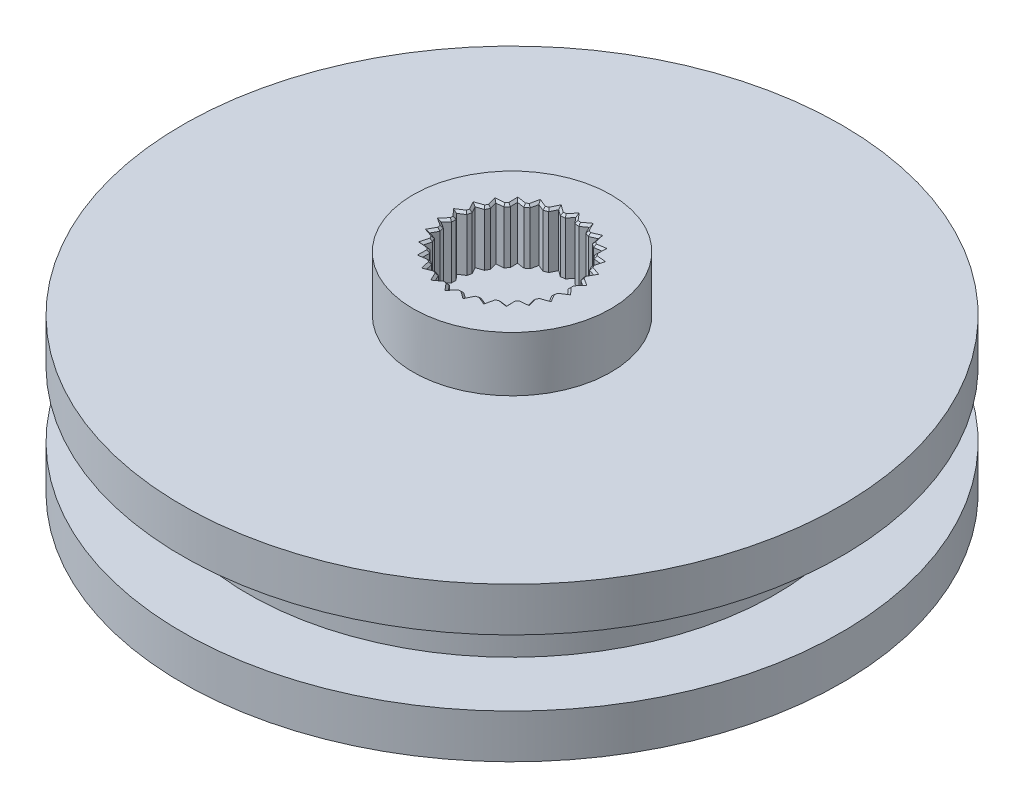
SolidWorks part; units mm, degrees
ref_plane "Front Plane" through (0, 0, 0) normal (0, 0, 1) x (1, 0, 0)
ref_plane "Top Plane" through (0, 0, 0) normal (0, 1, 0) x (1, 0, 0)
ref_plane "Right Plane" through (0, 0, 0) normal (1, 0, 0) x (0, 0, -1)
sketch "Sketch1" plane through (0, 0, 0) normal (0, 1, 0) x (1, 0, 0)
  line L0 (-4.9497, 4.9497) -> (4.9497, 4.9497) construction
  line L1 (4.9497, 4.9497) -> (4.9497, -4.9497) construction
  circle A0 centre (0, 0) radius 10
  circle A1 centre (-4.9497, 4.9497) radius 1.25
  circle A2 centre (4.9497, 4.9497) radius 1.25
  circle A3 centre (4.9497, -4.9497) radius 1.25
  circle A4 centre (-4.9497, -4.9497) radius 1.25
  circle A5 centre (0, 0) radius 7 construction
  circle A6 centre (0, 0) radius 1.5
  dimension "D1" = 20
  dimension "D2" = 2.5
  dimension "D3" = 3
  dimension "D4" = 14
extrude "Boss-Extrude1" add sketch "Sketch1" along normal blind 2
cosmetic thread "Cosmetic Thread1" parameters "D2"=3
cosmetic thread "Cosmetic Thread2" parameters "D2"=3
cosmetic thread "Cosmetic Thread3" parameters "D2"=3
cosmetic thread "Cosmetic Thread4" parameters "D2"=3
sketch "Sketch2" plane through (0, 2, 0) normal (0, 1, 0) x (1, 0, 0)
  circle A0 centre (0, 0) radius 4.5
  circle A1 centre (0, 0) radius 1.5 construction
  circle A2 centre (0, 0) radius 1.5
  dimension "D1" = 9
extrude "Boss-Extrude2" add sketch "Sketch2" along normal blind 2.5
sketch "Sketch3" plane through (0, 4.5, 0) normal (0, 1, 0) x (1, 0, 0)
  circle A0 centre (0, 0) radius 2.25
  dimension "D1" = 4.5
extrude "Cut-Extrude1" cut sketch "Sketch3" against normal blind 3.6
sketch "Sketch7" plane through (0, 4.5, 0) normal (0, 1, 0) x (1, 0, 0)
  line L0 (-1.035, 2.4395) -> (-0.843, 2.5123)
  line L1 (-0.843, 2.5123) -> (-0.7982, 2.6036)
  line L2 (-0.7982, 2.6036) -> (-0.694, 2.8157)
  line L3 (-0.694, 2.8157) -> (-0.5032, 2.6763)
  line L4 (-0.5032, 2.6763) -> (-0.4211, 2.6163)
  line L5 (-0.4211, 2.6163) -> (-0.2173, 2.6411)
  line L6 (-0.2173, 2.6411) -> (-0.1519, 2.719)
  line L7 (-0.1519, 2.719) -> (0, 2.9)
  line L8 (0, 2.9) -> (0.1519, 2.719)
  line L9 (0.1519, 2.719) -> (0.2173, 2.6411)
  line L10 (0.2173, 2.6411) -> (0.4211, 2.6163)
  line L11 (0.4211, 2.6163) -> (0.5032, 2.6763)
  line L12 (0.5032, 2.6763) -> (0.694, 2.8157)
  line L13 (0.694, 2.8157) -> (0.7982, 2.6036)
  line L14 (0.7982, 2.6036) -> (0.843, 2.5123)
  line L15 (0.843, 2.5123) -> (1.035, 2.4395)
  line L16 (1.035, 2.4395) -> (1.1291, 2.4781)
  line L17 (1.1291, 2.4781) -> (1.3477, 2.5678)
  line L18 (1.3477, 2.5678) -> (1.3981, 2.337)
  line L19 (1.3981, 2.337) -> (1.4197, 2.2376)
  line L20 (1.4197, 2.2376) -> (1.5887, 2.1209)
  line L21 (1.5887, 2.1209) -> (1.6893, 2.1359)
  line L22 (1.6893, 2.1359) -> (1.9231, 2.1707)
  line L23 (1.9231, 2.1707) -> (1.9167, 1.9345)
  line L24 (1.9167, 1.9345) -> (1.914, 1.8328)
  line L25 (1.914, 1.8328) -> (2.0501, 1.6791)
  line L26 (2.0501, 1.6791) -> (2.1514, 1.6696)
  line L27 (2.1514, 1.6696) -> (2.3867, 1.6474)
  line L28 (2.3867, 1.6474) -> (2.324, 1.4196)
  line L29 (2.324, 1.4196) -> (2.297, 1.3215)
  line L30 (2.297, 1.3215) -> (2.3924, 1.1397)
  line L31 (2.3924, 1.1397) -> (2.4884, 1.1062)
  line L32 (2.4884, 1.1062) -> (2.7115, 1.0284)
  line L33 (2.7115, 1.0284) -> (2.5962, 0.8221)
  line L34 (2.5962, 0.8221) -> (2.5465, 0.7334)
  line L35 (2.5465, 0.7334) -> (2.5956, 0.534)
  line L36 (2.6809, 0.4785) -> (2.5956, 0.534) construction
  line L37 (2.5956, 0.534) -> (2.6809, 0.4785)
  line L38 (2.6809, 0.4785) -> (2.8789, 0.3496)
  line L39 (2.6809, 0.4785) -> (2.8789, 0.3496)
  line L40 (2.7175, 0.177) -> (2.648, 0.1027)
  line L41 (2.648, 0.1027) -> (2.648, -0.1027)
  line L42 (2.648, -0.1027) -> (2.7175, -0.177)
  line L43 (2.7175, -0.177) -> (2.8789, -0.3496)
  line L44 (2.8789, -0.3496) -> (2.6809, -0.4785)
  line L45 (2.6809, -0.4785) -> (2.5956, -0.534)
  line L46 (2.5956, -0.534) -> (2.5465, -0.7334)
  line L47 (2.5465, -0.7334) -> (2.5962, -0.8221)
  line L48 (2.5962, -0.8221) -> (2.7115, -1.0284)
  line L49 (2.7115, -1.0284) -> (2.4884, -1.1062)
  line L50 (2.4884, -1.1062) -> (2.3924, -1.1397)
  line L51 (2.3924, -1.1397) -> (2.4884, -1.1062) construction
  line L52 (2.3924, -1.1397) -> (2.297, -1.3215)
  line L53 (2.297, -1.3215) -> (2.324, -1.4196)
  line L54 (2.324, -1.4196) -> (2.3867, -1.6474)
  line L55 (2.3867, -1.6474) -> (2.1514, -1.6696)
  line L56 (2.1514, -1.6696) -> (2.0501, -1.6791)
  line L57 (2.0501, -1.6791) -> (1.914, -1.8328)
  line L58 (1.914, -1.8328) -> (1.9167, -1.9345)
  line L59 (1.9167, -1.9345) -> (1.9231, -2.1707)
  line L60 (1.9231, -2.1707) -> (1.6893, -2.1359)
  line L61 (1.6893, -2.1359) -> (1.5887, -2.1209)
  line L62 (1.5887, -2.1209) -> (1.4197, -2.2376)
  line L63 (1.4197, -2.2376) -> (1.3981, -2.337)
  line L64 (1.3981, -2.337) -> (1.3477, -2.5678)
  line L65 (1.3477, -2.5678) -> (1.1291, -2.4781)
  line L66 (1.1291, -2.4781) -> (1.035, -2.4395)
  line L67 (1.035, -2.4395) -> (0.843, -2.5123)
  line L68 (0.843, -2.5123) -> (0.7982, -2.6036)
  line L69 (0.7982, -2.6036) -> (0.694, -2.8157)
  line L70 (0.694, -2.8157) -> (0.5032, -2.6763)
  line L71 (0.5032, -2.6763) -> (0.4211, -2.6163)
  line L72 (0.4211, -2.6163) -> (0.2173, -2.6411)
  line L73 (0.2173, -2.6411) -> (0.1519, -2.719)
  line L74 (0.1519, -2.719) -> (0, -2.9)
  line L75 (0, -2.9) -> (-0.1519, -2.719)
  line L76 (-0.1519, -2.719) -> (-0.2173, -2.6411)
  line L77 (-0.2173, -2.6411) -> (-0.4211, -2.6163)
  line L78 (-0.4211, -2.6163) -> (-0.5032, -2.6763)
  line L79 (-0.5032, -2.6763) -> (-0.694, -2.8157)
  line L80 (-0.694, -2.8157) -> (-0.7982, -2.6036)
  line L81 (-0.7982, -2.6036) -> (-0.843, -2.5123)
  line L82 (-0.843, -2.5123) -> (-1.035, -2.4395)
  line L83 (-1.035, -2.4395) -> (-1.1291, -2.4781)
  line L84 (-1.1291, -2.4781) -> (-1.3477, -2.5678)
  line L85 (-1.3477, -2.5678) -> (-1.3981, -2.337)
  line L86 (-1.3981, -2.337) -> (-1.4197, -2.2376)
  line L87 (-1.4197, -2.2376) -> (-1.5887, -2.1209)
  line L88 (-1.5887, -2.1209) -> (-1.6893, -2.1359)
  line L89 (-1.6893, -2.1359) -> (-1.9231, -2.1707)
  line L90 (-1.9231, -2.1707) -> (-1.9167, -1.9345)
  line L91 (-1.9167, -1.9345) -> (-1.914, -1.8328)
  line L92 (-1.914, -1.8328) -> (-2.0501, -1.6791)
  line L93 (-2.0501, -1.6791) -> (-2.1514, -1.6696)
  line L94 (-2.1514, -1.6696) -> (-2.3867, -1.6474)
  line L95 (-2.3867, -1.6474) -> (-2.324, -1.4196)
  line L96 (-2.324, -1.4196) -> (-2.297, -1.3215)
  line L97 (-2.297, -1.3215) -> (-2.3924, -1.1397)
  line L98 (-2.3924, -1.1397) -> (-2.4884, -1.1062)
  line L99 (-2.4884, -1.1062) -> (-2.7115, -1.0284)
  line L100 (-2.7115, -1.0284) -> (-2.5962, -0.8221)
  line L101 (-2.5962, -0.8221) -> (-2.5465, -0.7334)
  line L102 (-2.5465, -0.7334) -> (-2.5956, -0.534)
  line L103 (-2.5956, -0.534) -> (-2.6809, -0.4785)
  line L104 (-2.6809, -0.4785) -> (-2.8789, -0.3496)
  line L105 (-2.8789, -0.3496) -> (-2.7175, -0.177)
  line L106 (-2.7175, -0.177) -> (-2.648, -0.1027)
  line L107 (-2.648, -0.1027) -> (-2.648, 0.1027)
  line L108 (-2.648, 0.1027) -> (-2.7175, 0.177)
  line L109 (-2.7175, 0.177) -> (-2.8789, 0.3496)
  line L110 (-2.8789, 0.3496) -> (-2.6809, 0.4785)
  line L111 (-2.6809, 0.4785) -> (-2.5956, 0.534)
  line L112 (-2.5956, 0.534) -> (-2.5465, 0.7334)
  line L113 (-2.5465, 0.7334) -> (-2.5962, 0.8221)
  line L114 (-2.5962, 0.8221) -> (-2.7115, 1.0284)
  line L115 (-2.7115, 1.0284) -> (-2.4884, 1.1062)
  line L116 (-2.4884, 1.1062) -> (-2.3924, 1.1397)
  line L117 (-2.3924, 1.1397) -> (-2.297, 1.3215)
  line L118 (-2.297, 1.3215) -> (-2.324, 1.4196)
  line L119 (-2.324, 1.4196) -> (-2.3867, 1.6474)
  line L120 (-2.3867, 1.6474) -> (-2.1514, 1.6696)
  line L121 (-2.1514, 1.6696) -> (-2.0501, 1.6791)
  line L122 (-2.0501, 1.6791) -> (-1.914, 1.8328)
  line L123 (-1.914, 1.8328) -> (-1.9167, 1.9345)
  line L124 (-1.9167, 1.9345) -> (-1.9231, 2.1707)
  line L125 (-1.9231, 2.1707) -> (-1.6893, 2.1359)
  line L126 (-1.6893, 2.1359) -> (-1.5887, 2.1209)
  line L127 (-1.5887, 2.1209) -> (-1.4197, 2.2376)
  line L128 (-1.4197, 2.2376) -> (-1.3981, 2.337)
  line L129 (-1.3981, 2.337) -> (-1.3477, 2.5678)
  line L130 (-1.3477, 2.5678) -> (-1.1291, 2.4781)
  line L131 (-1.1291, 2.4781) -> (-1.035, 2.4395)
  line L132 (-0.843, 2.5123) -> (-0.7982, 2.6036)
  line L133 (-0.694, 2.8157) -> (-0.5032, 2.6763)
  line L134 (-0.4211, 2.6163) -> (-0.2173, 2.6411)
  line L135 (-0.1519, 2.719) -> (0, 2.9)
  line L136 (0.1519, 2.719) -> (0.2173, 2.6411)
  line L137 (0.4211, 2.6163) -> (0.5032, 2.6763)
  line L138 (0.694, 2.8157) -> (0.7982, 2.6036)
  line L139 (1.035, 2.4395) -> (1.3477, 2.5678)
  line L140 (1.3981, 2.337) -> (1.4197, 2.2376)
  line L141 (1.5887, 2.1209) -> (1.6893, 2.1359)
  line L142 (1.9231, 2.1707) -> (1.9167, 1.9345)
  line L143 (1.914, 1.8328) -> (2.0501, 1.6791)
  line L144 (2.1514, 1.6696) -> (2.3867, 1.6474)
  line L145 (2.324, 1.4196) -> (2.297, 1.3215)
  line L146 (2.3924, 1.1397) -> (2.7115, 1.0284)
  line L147 (2.5962, 0.8221) -> (2.5465, 0.7334)
  line L148 (2.8789, 0.3496) -> (2.7175, 0.177)
extrude "Cut-Extrude2" cut sketch "Sketch7" against normal up to surface (3.6 mm away) contours L148 L38 L37 L35 L34 L33 L32 L31 L30 L29 L28 L27 L26 L25 L24 L23 L22 L21 L20 L19 L18 L17 L16 L15 L14 L13 L12 L11 L10 L9 L8 L7 L6 L5 L4 L3 L2 L1 L0 L131 L130 L129 L128 L127 L126 L125 L124 L123 L122 L121 L120 up to face at (0, 0.9, 1.5)
chamfer "Chamfer1" distance 0.1 angle 45 78 edges at (-2.629, 4.5, -0.8809) (-2.5711, 4.5, -0.6337) (-2.7372, 4.5, -0.4418) (-2.7634, 4.5, -0.2261) (-2.648, 4.5, 0) (-2.7634, 4.5, 0.2261) (-2.7372, 4.5, 0.4418) (-2.5711, 4.5, 0.6337) (-2.629, 4.5, 0.8809) (-2.552, 4.5, 1.084) (-2.3447, 4.5, 1.2306) (-2.3418, 4.5, 1.4844) (-2.2184, 4.5, 1.6632) (-1.9821, 4.5, 1.756) (-1.9185, 4.5, 2.0017) (-1.7559, 4.5, 2.1458) (-1.5042, 4.5, 2.1793) (-1.3837, 4.5, 2.4027) (-1.1913, 4.5, 2.5037) (-0.939, 4.5, 2.4759) (-0.7685, 4.5, 2.664) (-0.5576, 4.5, 2.716) (-0.3192, 4.5, 2.6287) (-0.1086, 4.5, 2.7705) (0.1086, 4.5, 2.7705) (0.3192, 4.5, 2.6287) (0.5576, 4.5, 2.716) (0.7685, 4.5, 2.664) (0.939, 4.5, 2.4759) (1.1913, 4.5, 2.5037) (1.3837, 4.5, 2.4027) (1.5042, 4.5, 2.1793) (1.7559, 4.5, 2.1458) (1.9185, 4.5, 2.0017) (1.9821, 4.5, 1.756) (2.2184, 4.5, 1.6632) (2.3418, 4.5, 1.4844) (2.3447, 4.5, 1.2306) (2.552, 4.5, 1.084) (2.629, 4.5, 0.8809) (2.5711, 4.5, 0.6337) (2.7372, 4.5, 0.4418) (2.7634, 4.5, 0.2261) (2.648, 4.5, 0) (2.7634, 4.5, -0.2261) (2.7372, 4.5, -0.4418) (2.5711, 4.5, -0.6337) (2.629, 4.5, -0.8809) (2.552, 4.5, -1.084) (2.3447, 4.5, -1.2306) (2.3418, 4.5, -1.4844) (2.2184, 4.5, -1.6632) (1.9821, 4.5, -1.756) (1.9185, 4.5, -2.0017) (1.7559, 4.5, -2.1458) (1.5042, 4.5, -2.1793) (1.3837, 4.5, -2.4027) (1.1913, 4.5, -2.5037) (0.939, 4.5, -2.4759) (0.7685, 4.5, -2.664) (0.5576, 4.5, -2.716) (0.3192, 4.5, -2.6287) (0.1086, 4.5, -2.7705) (-0.1086, 4.5, -2.7705) (-0.3192, 4.5, -2.6287) (-0.5576, 4.5, -2.716) (-0.7685, 4.5, -2.664) (-0.939, 4.5, -2.4759) (-1.1913, 4.5, -2.5037) (-1.3837, 4.5, -2.4027) (-1.5042, 4.5, -2.1793) (-1.7559, 4.5, -2.1458) (-1.9185, 4.5, -2.0017) (-1.9821, 4.5, -1.756) (-2.2184, 4.5, -1.6632) (-2.3418, 4.5, -1.4844) (-2.3447, 4.5, -1.2306) (-2.552, 4.5, -1.084)
sketch "Sketch8" plane through (0, 0, 0) normal (0, -1, 0) x (1, 0, 0)
  circle A0 centre (0, 0) radius 10
extrude "Cut-Extrude3" cut sketch "Sketch8" against normal blind 2
sketch "Sketch9" plane through (0, 2, 0) normal (0, -1, 0) x (1, 0, 0)
  circle A0 centre (0, 0) radius 15
  dimension "D1" = 30
extrude "Boss-Extrude3" add sketch "Sketch9" along normal blind 2
sketch "Sketch10" plane through (0, 0, 0) normal (0, -1, 0) x (1, 0, 0)
  circle A0 centre (0, 0) radius 12
  dimension "D1" = 24
extrude "Boss-Extrude4" add sketch "Sketch10" along normal blind 3
sketch "Sketch11" plane through (0, -3, 0) normal (0, -1, 0) x (1, 0, 0)
  circle A0 centre (0, 0) radius 15
  dimension "D1" = 30
extrude "Boss-Extrude5" add sketch "Sketch11" along normal blind 2
